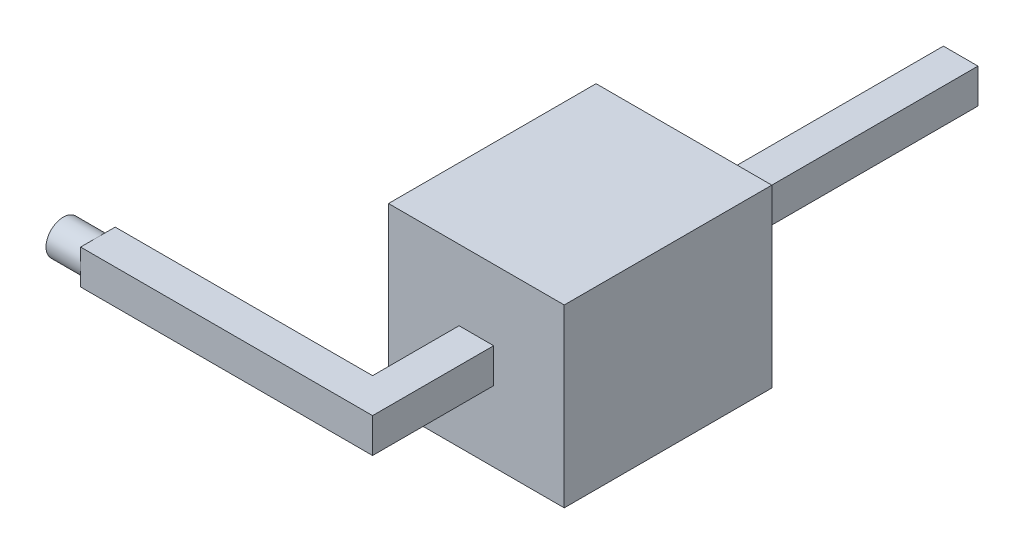
SolidWorks part; units mm, degrees
ref_plane "Front Plane" through (0, 0, 0) normal (0, 0, 1) x (1, 0, 0)
ref_plane "Top Plane" through (0, 0, 0) normal (0, 1, 0) x (1, 0, 0)
ref_plane "Right Plane" through (0, 0, 0) normal (1, 0, 0) x (0, 0, -1)
sketch "Sketch1" plane through (0, 0, 0) normal (0, 1, 0) x (1, 0, 0)
  line L1 (0, 0) -> (4.72, 0)
  line L2 (0, 0) -> (0, 0.5)
  line L3 (0, 0.5) -> (4.22, 0.5)
  line L4 (4.72, 0) -> (4.72, 3.65)
  line L6 (4.72, 3.65) -> (4.72, 8.75)
  line L7 (4.72, 8.75) -> (4.22, 8.75)
  line L8 (4.22, 0.5) -> (4.22, 8.75)
  point P8 (0, 0.25)
  point P9 (0, 0)
  dimension "D1" = 0.5
  dimension "D2" = 8.5
  dimension "D3" = 4.72
extrude "Boss-Extrude1" add sketch "Sketch1" along normal blind 0.5
ref_plane "Plane1" through (0, 0, -4.75) normal (0, 0, -1) x (-1, 0, 0)
sketch "Sketch2" plane through (0, 0, -4.75) normal (0, 0, -1) x (-1, 0, 0)
  line L0 (-4.22, 0) -> (-4.72, 0.5) construction
  line L1 (-4.72, 0.5) -> (-4.72, 0) construction
  line L2 (-4.72, 0.5) -> (-4.22, 0.5) construction
  line L4 (-3.2, -1.02) -> (-5.74, -1.02)
  line L5 (-3.2, -1.02) -> (-3.2, 1.52)
  line L6 (-3.2, 1.52) -> (-5.74, 1.52)
  line L7 (-5.74, -1.02) -> (-5.74, 1.52)
  line L8 (-3.2, -1.02) -> (-5.74, 1.52) construction
  line L9 (-3.2, 1.52) -> (-5.74, -1.02) construction
  point P8 (-4.47, 0.25)
  point P9 (-4.47, 0.25)
  dimension "D1" = 2.54
extrude "Boss-Extrude2" add sketch "Sketch2" against normal blind 3
sketch "Sketch3" plane through (0, 0, 0) normal (-1, 0, 0) x (0, 0, 1)
  line L0 (-0.5, 0) -> (0, 0.5) construction
  line L1 (-0.5, 0.5) -> (0, 0.5) construction
  circle A0 centre (-0.25, 0.25) radius 0.25
  point P6 (0, 0)
extrude "Cut-Extrude1" cut sketch "Sketch3" against normal blind 0.5 flip side to cut
